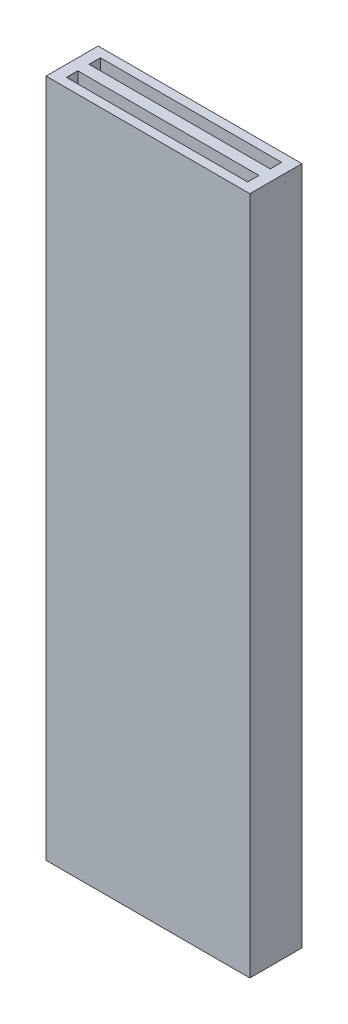
SolidWorks part; units mm, degrees
ref_plane "Front Plane" through (0, 0, 0) normal (0, 0, 1) x (1, 0, 0)
ref_plane "Top Plane" through (0, 0, 0) normal (0, 1, 0) x (1, 0, 0)
ref_plane "Right Plane" through (0, 0, 0) normal (1, 0, 0) x (0, 0, -1)
sketch "Sketch1" plane through (0, 0, 0) normal (0, 1, 0) x (1, 0, 0)
  line L1 (-4.5, -1.15) -> (4.5, -1.15)
  line L2 (-4.5, -1.15) -> (-4.5, 1.15)
  line L3 (-4.5, 1.15) -> (4.5, 1.15)
  line L4 (4.5, -1.15) -> (4.5, 1.15)
  line L5 (-4.5, -1.15) -> (4.5, 1.15) construction
  line L6 (-4.5, 1.15) -> (4.5, -1.15) construction
  point P0 (0, 0)
  dimension "D1" = 9
  dimension "D2" = 2.3
extrude "Boss-Extrude1" add sketch "Sketch1" along normal mid plane 30
sketch "Sketch2" plane through (0, 15, 0) normal (0, 1, 0) x (1, 0, 0)
  line L1 (-4, 0.25) -> (4, 0.25)
  line L2 (-4, 0.25) -> (-4, 0.75)
  line L3 (-4, 0.75) -> (4, 0.75)
  line L4 (4, 0.25) -> (4, 0.75)
  line L5 (-4, 0.25) -> (4, 0.75) construction
  line L6 (-4, 0.75) -> (4, 0.25) construction
  point P0 (0, 0.5)
  dimension "D1" = 0.5
  dimension "D2" = 8
  dimension "D3" = 0
  dimension "D4" = 0.5
extrude "Cut-Extrude1" cut sketch "Sketch2" against normal through all and the other way through all
mirror "Mirror1" about plane through (0, 0, 0) normal (0, 0, 1) of "Cut-Extrude1"
